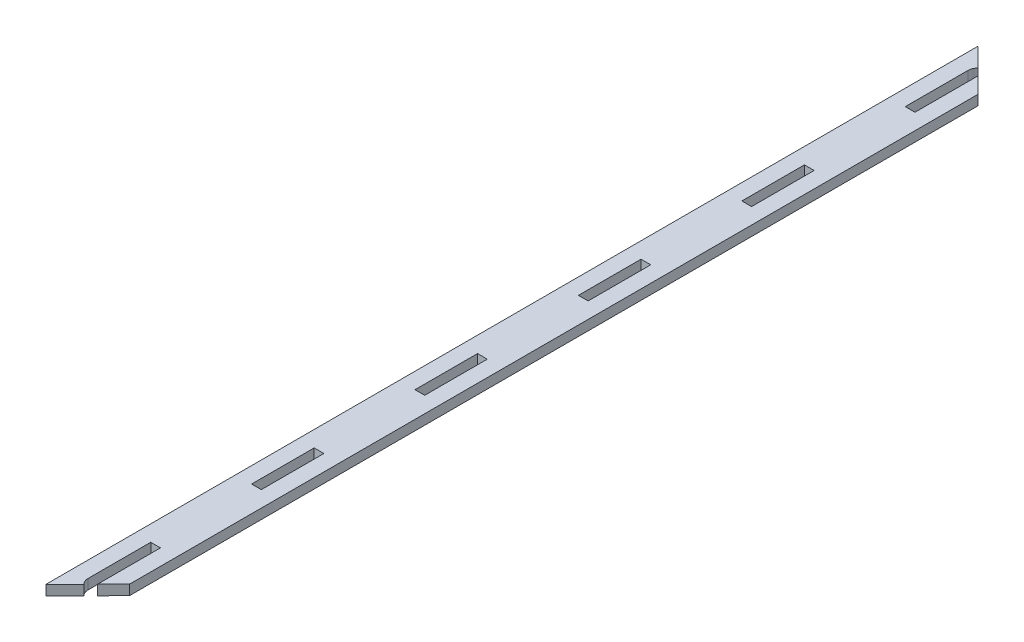
SolidWorks part; units mm, degrees
material "Acrylic (Medium-high impact)"
ref_plane "Front Plane" through (0, 0, 0) normal (0, 0, 1) x (1, 0, 0)
ref_plane "Top Plane" through (0, 0, 0) normal (0, 1, 0) x (1, 0, 0)
ref_plane "Right Plane" through (0, 0, 0) normal (1, 0, 0) x (0, 0, -1)
sketch "Sketch1" plane through (0, 0, 0) normal (0, 1, 0) x (1, 0, 0)
  line L2 (0, 296.4) -> (0, 0)
  line L52 (-5.9521, 8.2) -> (8.175, 8.2) construction
  line L73 (8.175, 8.2) -> (8.175, 5.025)
  line L81 (8.175, 8.2) -> (5, 8.2)
  line L82 (8.175, 8.2) -> (8.175, 28.2)
  line L83 (5, 8.2) -> (5, 28.2)
  line L84 (8.175, 28.2) -> (5, 28.2)
  line L85 (8.175, 60.205) -> (5, 60.205)
  line L86 (8.175, 60.205) -> (8.175, 80.205)
  line L87 (5, 60.205) -> (5, 80.205)
  line L88 (8.175, 80.205) -> (5, 80.205)
  line L89 (8.175, 112.21) -> (5, 112.21)
  line L90 (8.175, 112.21) -> (8.175, 132.21)
  line L91 (5, 112.21) -> (5, 132.21)
  line L92 (8.175, 132.21) -> (5, 132.21)
  line L93 (8.175, 164.215) -> (5, 164.215)
  line L94 (8.175, 164.215) -> (8.175, 184.215)
  line L95 (5, 164.215) -> (5, 184.215)
  line L96 (8.175, 184.215) -> (5, 184.215)
  line L97 (8.175, 216.22) -> (5, 216.22)
  line L98 (8.175, 216.22) -> (8.175, 236.22)
  line L99 (5, 216.22) -> (5, 236.22)
  line L100 (8.175, 236.22) -> (5, 236.22)
  line L101 (8.175, 268.225) -> (5, 268.225)
  line L102 (8.175, 268.225) -> (8.175, 288.225)
  line L103 (5, 268.225) -> (5, 288.225)
  line L104 (8.175, 288.225) -> (5, 288.225)
  line L151 (8.175, 288.225) -> (8.175, 291.4)
  line L158 (0, 296.4) -> (13.175, 283.225)
  line L159 (13.175, 283.225) -> (13.175, 13.2153)
  line L160 (13.175, 13.2153) -> (0, 0)
  arc A0 (5, 8.2) -> (8.175, 5.025) centre (8.175, 8.2) ccw
  arc A3 (5, 288.225) -> (8.175, 291.4) centre (8.175, 288.225) cw
  point P100 (0, 0)
  point P102 (14.2226, 15.9788)
  dimension "D2" = 3.175
  dimension "D5" = 20
  dimension "D8" = 5
  dimension "D15" = 5
  dimension "D3" = 18.6608
  dimension "D4" = 32.005
  dimension "D6" = 18.6323
  dimension "D7" = 6
extrude "Boss-Extrude1" add sketch "Sketch1" along normal blind 3.175
sketch "Sketch10" plane through (0, 3.175, 0) normal (0, 1, 0) x (1, 0, 0)
  line L24 (-0.0406, 296.4981) -> (-0.0406, -0.0983)
  line L25 (-0.0406, -0.0983) -> (5.991, 5.9518)
  line L26 (5.0406, 8.2) -> (5.0406, 28.1594)
  line L27 (5.0406, 28.1594) -> (8.1344, 28.1594)
  line L28 (8.1344, 28.1594) -> (8.1344, 8.1017)
  line L29 (8.1344, 8.1017) -> (13.2156, 13.1985)
  line L30 (13.2156, 13.1985) -> (13.2156, 283.2418)
  line L31 (13.2156, 283.2418) -> (8.1344, 288.3231)
  line L32 (8.1344, 288.3231) -> (8.1344, 268.2656)
  line L33 (8.1344, 268.2656) -> (5.0406, 268.2656)
  line L34 (5.0406, 268.2656) -> (5.0406, 288.225)
  line L35 (5.9876, 290.4699) -> (-0.0406, 296.4981)
  line L36 (-0.0406, 296.4981) -> (-0.0406, -0.0983)
  line L37 (-0.0406, -0.0983) -> (5.991, 5.9518)
  line L38 (5.0406, 8.2) -> (5.0406, 28.1594)
  line L39 (5.0406, 28.1594) -> (8.1344, 28.1594)
  line L40 (8.1344, 28.1594) -> (8.1344, 8.1017)
  line L41 (8.1344, 8.1017) -> (13.2156, 13.1985)
  line L42 (13.2156, 13.1985) -> (13.2156, 283.2418)
  line L43 (13.2156, 283.2418) -> (8.1344, 288.3231)
  line L44 (8.1344, 288.3231) -> (8.1344, 268.2656)
  line L45 (8.1344, 268.2656) -> (5.0406, 268.2656)
  line L46 (5.0406, 268.2656) -> (5.0406, 288.225)
  line L47 (5.9876, 290.4699) -> (-0.0406, 296.4981)
  line L463 (8.1344, 216.2606) -> (8.1344, 236.1794)
  line L464 (5.0406, 216.2606) -> (8.1344, 216.2606)
  line L465 (5.0406, 236.1794) -> (5.0406, 216.2606)
  line L466 (8.1344, 236.1794) -> (5.0406, 236.1794)
  line L467 (8.1344, 216.2606) -> (8.1344, 236.1794)
  line L468 (5.0406, 216.2606) -> (8.1344, 216.2606)
  line L469 (5.0406, 236.1794) -> (5.0406, 216.2606)
  line L470 (8.1344, 236.1794) -> (5.0406, 236.1794)
  line L481 (5.0406, 164.2556) -> (8.1344, 164.2556)
  line L482 (8.1344, 164.2556) -> (8.1344, 184.1744)
  line L483 (5.0406, 184.1744) -> (5.0406, 164.2556)
  line L484 (8.1344, 184.1744) -> (5.0406, 184.1744)
  line L485 (5.0406, 164.2556) -> (8.1344, 164.2556)
  line L486 (8.1344, 164.2556) -> (8.1344, 184.1744)
  line L487 (5.0406, 184.1744) -> (5.0406, 164.2556)
  line L488 (8.1344, 184.1744) -> (5.0406, 184.1744)
  line L499 (5.0406, 112.2506) -> (8.1344, 112.2506)
  line L500 (8.1344, 112.2506) -> (8.1344, 132.1694)
  line L501 (5.0406, 132.1694) -> (5.0406, 112.2506)
  line L502 (8.1344, 132.1694) -> (5.0406, 132.1694)
  line L503 (5.0406, 112.2506) -> (8.1344, 112.2506)
  line L504 (8.1344, 112.2506) -> (8.1344, 132.1694)
  line L505 (5.0406, 132.1694) -> (5.0406, 112.2506)
  line L506 (8.1344, 132.1694) -> (5.0406, 132.1694)
  line L517 (5.0406, 60.2456) -> (8.1344, 60.2456)
  line L518 (8.1344, 60.2456) -> (8.1344, 80.1644)
  line L519 (5.0406, 80.1644) -> (5.0406, 60.2456)
  line L520 (8.1344, 80.1644) -> (5.0406, 80.1644)
  line L521 (5.0406, 60.2456) -> (8.1344, 60.2456)
  line L522 (8.1344, 60.2456) -> (8.1344, 80.1644)
  line L523 (5.0406, 80.1644) -> (5.0406, 60.2456)
  line L524 (8.1344, 80.1644) -> (5.0406, 80.1644)
  arc A4 (5.0406, 8.2) -> (5.991, 5.9518) centre (8.175, 8.2) ccw
  arc A5 (5.9876, 290.4699) -> (5.0406, 288.225) centre (8.175, 288.225) ccw
  arc A6 (5.0406, 8.2) -> (5.991, 5.9518) centre (8.175, 8.2) ccw
  arc A7 (5.9876, 290.4699) -> (5.0406, 288.225) centre (8.175, 288.225) ccw
  dimension "D1" = 0.0406
  dimension "D2" = 0.0406
  dimension "D3" = 0.0406
  dimension "D4" = 0.0406
  dimension "D5" = 0.0406
extrude "Boss-Extrude2" add sketch "Sketch10" against normal up to surface (3.175 mm away) up to face at (6.5875, 0, -226.22)
equation "\"stepper width\"=4.23"
equation "\"stepper hole disctance\"= 3.1"
equation "\"stepper hole diameter\"=0.34"
equation "\"stepper shaft hole\"=2.4"
equation "\"tooth width\"=0.4"
equation "\"tooth thickness\"= 0.3175"
equation "\"tooth to side\"=0.75"
equation "\"motor chamber height\"= 6"
equation "\"enclosure length\"= 22 + 6"
equation "\"platform diameter\"= 9"
equation "\"teeth width\"=0.3175"
equation "\"teeth lenght\"=2"
equation "\"tower width\"=7.7"
equation "\"support width\"=1"
equation "\"trial hole spacing\"= 0.75"
equation "\"mounting distance\"= 4"
equation "\"D1@Block1\"=\"tooth width\""
equation "\"D2@Block1\"=\"tooth thickness\""
equation "\"D3@Block1\"=\"tooth to side\""
equation "\"half belt distance\"=5.5"
equation "\"holder distance to wall\"= 2.25"
equation "\"D1@Block2\"=\"tooth width\""
equation "\"D2@Block2\"=\"tooth thickness\""
equation "\"D3@Block2\"=\"tooth to side\""
equation "\"D4@Block2\"=\"tooth to side\""
equation "\"bearing outer diameter\"= 1.6"
equation "\"half belt length\"=5.5"
equation "\"screw hole diameter\"=0.351"
equation "\"distance between screw hles\"=3"
equation "\"spinner to stack center to center\"= 15.5"
equation "\"D5@Sketch1\"=\"teeth lenght\""
equation "\"D2@Sketch1\"=\"teeth width\""
equation "\"stack to elevator center to center\"= 21.64"
equation "\"D1@Boss-Extrude1\"=\"tooth thickness\""
equation "\"D1@Block6\"=\"tooth thickness\""
